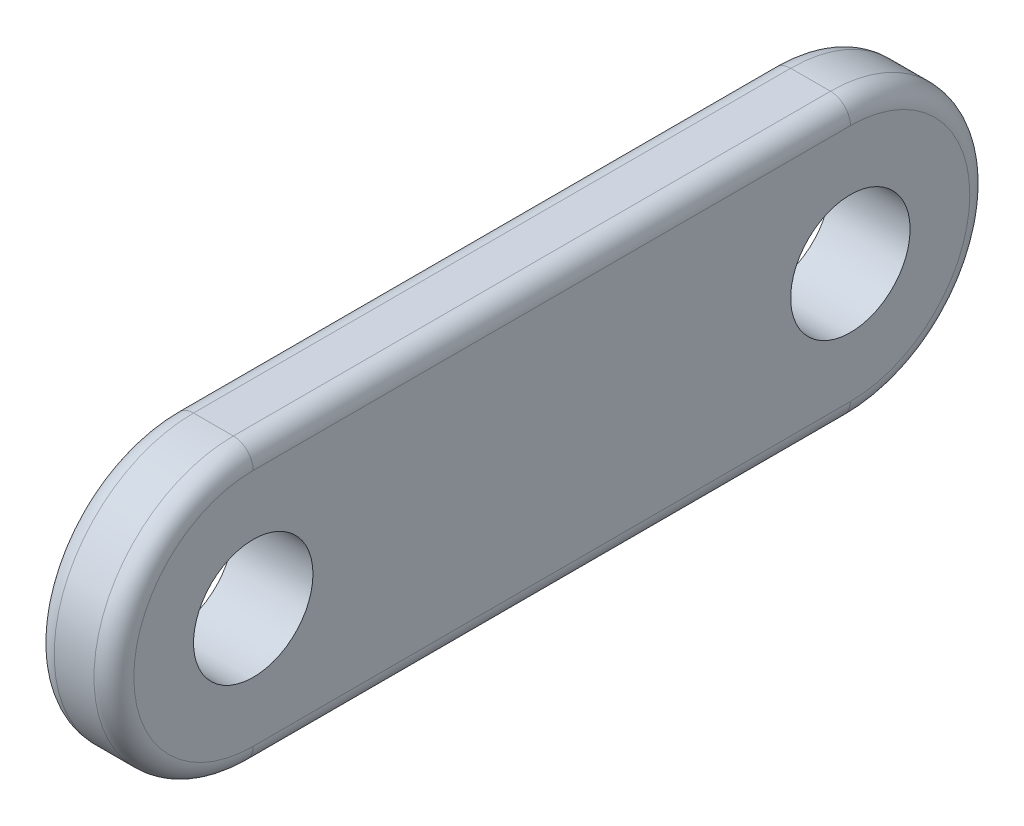
SolidWorks part; units mm, degrees
ref_plane "前视基准面" through (0, 0, 0) normal (0, 0, 1) x (1, 0, 0)
ref_plane "上视基准面" through (0, 0, 0) normal (0, 1, 0) x (1, 0, 0)
ref_plane "右视基准面" through (0, 0, 0) normal (1, 0, 0) x (0, 0, -1)
sketch "草图1" plane through (0, 0, 0) normal (1, 0, 0) x (0, 0, -1)
  line L0 (-15, 0) -> (15, 0) construction
  line L1 (-15, 7) -> (15, 7)
  line L2 (-15, -7) -> (15, -7)
  arc A0 (-15, 7) -> (-15, -7) centre (-15, 0) ccw
  arc A1 (15, -7) -> (15, 7) centre (15, 0) ccw
  circle A2 centre (-15, 0) radius 3
  circle A3 centre (15, 0) radius 3
  point P2 (0, 0)
  dimension "D2" = 7
  dimension "D3" = 6
  dimension "D1" = 30
extrude "凸台-拉伸1" add sketch "草图1" along normal blind 4
fillet "圆角1" radius 1 8 edges at (0, 0, -22) (0, -7, 0) (0, 0, 22) (4, 0, -22) (4, -7, 0) (4, 0, 22) (0, 7, 0) (4, 7, 0)
